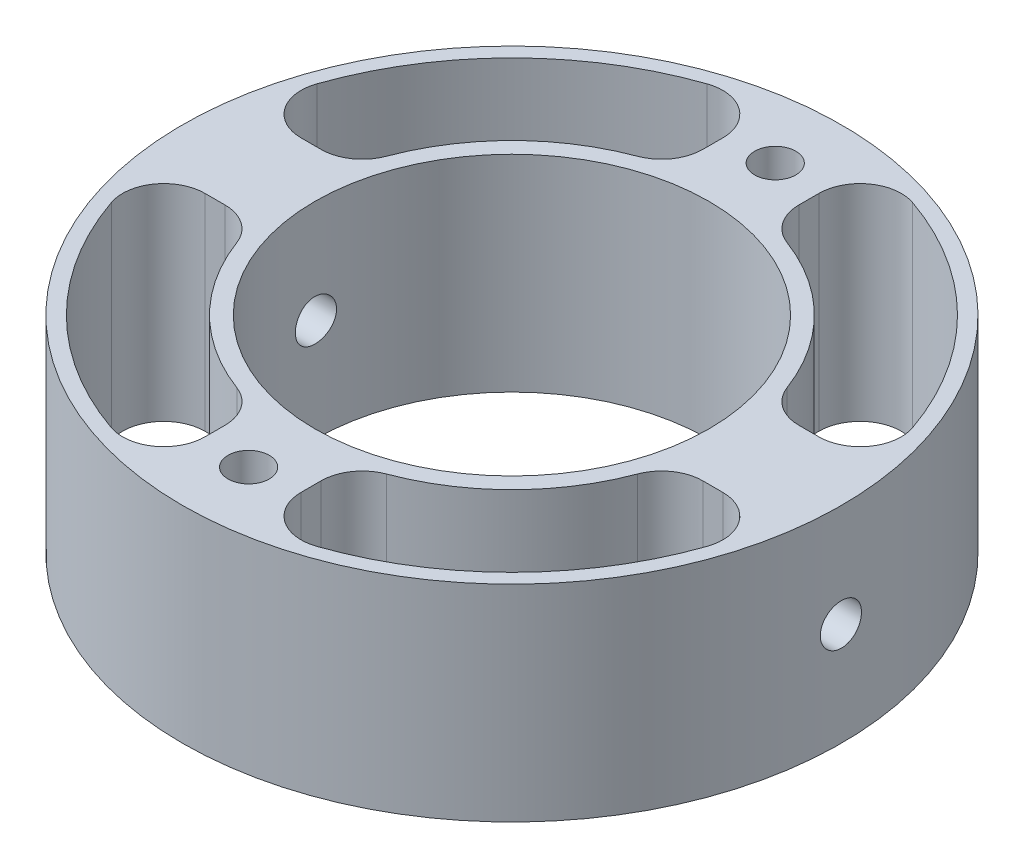
SolidWorks part; units mm, degrees
ref_plane "Front Plane" through (0, 0, 0) normal (0, 0, 1) x (1, 0, 0)
ref_plane "Top Plane" through (0, 0, 0) normal (0, 1, 0) x (1, 0, 0)
ref_plane "Right Plane" through (0, 0, 0) normal (1, 0, 0) x (0, 0, -1)
sketch "Sketch3" plane through (0, 0, 0) normal (0, 1, 0) x (1, 0, 0)
  circle A0 centre (0, 0) radius 24
  circle A1 centre (0, 0) radius 14.35
  dimension "D1" = 48
  dimension "D2" = 28.7
extrude "Boss-Extrude1" add sketch "Sketch3" along normal blind 15
sketch "Sketch4" plane through (0, 0, 0) normal (1, 0, 0) x (0, 0, -1)
  circle A0 centre (0, 7.5) radius 1.5
  dimension "D1" = 3
  dimension "D2" = 7.5
extrude "Cut-Extrude2" cut sketch "Sketch4" against normal blind 100 from offset 50
sketch "Sketch5" plane through (0, 15, 0) normal (0, 1, 0) x (1, 0, 0)
  circle A0 centre (0, 19.175) radius 1.5
  circle A3 centre (0, -19.175) radius 1.5
  dimension "D1" = 3
  dimension "D4" = 3
  dimension "D2" = 19.175
  dimension "D3" = 19.175
extrude "Cut-Extrude3" cut sketch "Sketch5" against normal blind 100
sketch "Sketch7" plane through (0, 15, 0) normal (0, 1, 0) x (1, 0, 0)
  line L0 (3.5, 15.175) -> (3.5, 22.675)
  line L1 (15.175, 3.5) -> (22.675, 3.5)
  arc A0 (3.5, 22.675) -> (22.675, 3.5) centre (0, 0) cw
  arc A1 (3.5, 15.175) -> (15.175, 3.5) centre (0, 0) cw
  dimension "D1" = 3.5
  dimension "D2" = 22.675
  dimension "D4" = 3.5
  dimension "D3" = 3.5
  dimension "D5" = 15.175
  dimension "D6" = 3.5
extrude "Cut-Extrude6" cut sketch "Sketch7" against normal blind 26
sketch "Sketch9" plane through (0, 15, 0) normal (0, 1, 0) x (1, 0, 0)
  line L0 (15.175, -3.5) -> (22.675, -3.5)
  line L1 (3.5, -15.175) -> (3.5, -22.675)
  arc A0 (15.175, -3.5) -> (3.5, -15.175) centre (0, 0) cw
  arc A1 (22.675, -3.5) -> (3.5, -22.675) centre (0, 0) cw
  dimension "D3" = 3.5
  dimension "D6" = 3.5
  dimension "D1" = 15.175
  dimension "D2" = 3.5
  dimension "D4" = 22.675
  dimension "D5" = 3.5
extrude "Cut-Extrude7" cut sketch "Sketch9" against normal blind 26
sketch "Sketch10" plane through (0, 15, 0) normal (0, 1, 0) x (1, 0, 0)
  line L0 (-3.5, 15.175) -> (-3.5, 22.675)
  line L1 (-22.675, 3.5) -> (-15.175, 3.5)
  arc A0 (-3.5, 15.175) -> (-15.175, 3.5) centre (0, 0) ccw
  arc A1 (-3.5, 22.675) -> (-22.675, 3.5) centre (0, 0) ccw
  dimension "D1" = 3.5
  dimension "D4" = 3.5
  dimension "D3" = 3.5
  dimension "D6" = 3.5
  dimension "D2" = 15.175
  dimension "D5" = 22.675
extrude "Cut-Extrude8" cut sketch "Sketch10" against normal blind 26
sketch "Sketch11" plane through (0, 15, 0) normal (0, 1, 0) x (1, 0, 0)
  line L0 (-15.175, -3.5) -> (-22.675, -3.5)
  line L1 (-3.5, -15.175) -> (-3.5, -22.675)
  arc A0 (-22.675, -3.5) -> (-3.5, -22.675) centre (0, 0) ccw
  arc A1 (-3.5, -15.175) -> (-15.175, -3.5) centre (0, 0) cw
  dimension "D4" = 3.5
  dimension "D3" = 3.5
  dimension "D2" = 3.5
  dimension "D5" = 3.5
  dimension "D1" = 22.675
  dimension "D6" = 15.175
extrude "Cut-Extrude9" cut sketch "Sketch11" against normal blind 26
fillet "Fillet5" radius 3 16 edges at (3.5, 7.5, -15.175) (3.5, 7.5, -22.675) (15.175, 7.5, -3.5) (22.675, 7.5, -3.5) (15.175, 7.5, 3.5) (22.675, 7.5, 3.5) (3.5, 7.5, 15.175) (3.5, 7.5, 22.675) (-3.5, 7.5, 22.675) (-3.5, 7.5, 15.175) (-22.675, 7.5, 3.5) (-15.175, 7.5, 3.5) (-15.175, 7.5, -3.5) (-22.675, 7.5, -3.5) (-3.5, 7.5, -15.175) (-3.5, 7.5, -22.675)
equation "\"TubeInnerDiameter\"= 48mm"
equation "\"MotorCasingDiameter\"= 28.7mm"
equation "\"BoltDiameter\"= 3mm"
equation "\"SpacerHeight\"= 15mm"
equation "\"D1@Sketch3\"=\"TubeInnerDiameter\""
equation "\"D1@Boss-Extrude1\"=\"SpacerHeight\""
equation "\"D1@Sketch4\"=\"BoltDiameter\""
equation "\"D2@Sketch4\"=\"SpacerHeight\"/2"
equation "\"TopBoltDiameter\"= 3mm"
equation "\"D1@Sketch5\"=\"TopBoltDiameter\""
equation "\"D2@Sketch5\"=(\"TubeInnerDiameter\"/2-\"MotorCasingDiameter\"/2)/2+\"MotorCasingDiameter\"/2"
equation "\"D4@Sketch5\"=\"TopBoltDiameter\""
equation "\"D3@Sketch5\"=(\"TubeInnerDiameter\"/2-\"MotorCasingDiameter\"/2)/2+\"MotorCasingDiameter\"/2"
equation "\"PressureChannelWidth\"= 8mm"
equation "\"IgniterChannelDiameter\"= 2.8mm"
equation "\"D1@Sketch7\"=\"TopBoltDiameter\"/2+\"BoltChannelSeparation\""
equation "\"D4@Sketch7\"=\"BoltDiameter\"/2+\"BoltChannelSeparation\""
equation "\"BoltChannelSeparation\" = 2mm"
equation "\"D3@Sketch7\"=\"TopBoltDiameter\"/2+\"BoltChannelSeparation\""
equation "\"D5@Sketch7\"=(\"TubeInnerDiameter\"/2+\"MotorCasingDiameter\"/2)/2-\"PressureChannelWidth\"/2"
equation "\"D6@Sketch7\"=\"BoltDiameter\"/2+\"BoltChannelSeparation\""
equation "\"D2@Sketch7\"=(\"TubeInnerDiameter\"/2+\"MotorCasingDiameter\"/2)/2+\"PressureChannelWidth\"/2-0.5"
equation "\"D2@Sketch3\"=\"MotorCasingDiameter\""
equation "\"ChamferRadius\"= 3mm"
equation "\"D1@Sketch9\"=(\"TubeInnerDiameter\"/2+\"MotorCasingDiameter\"/2)/2-\"PressureChannelWidth\"/2"
equation "\"D2@Sketch9\"=\"BoltDiameter\"/2+\"BoltChannelSeparation\""
equation "\"D3@Sketch9\"=\"BoltDiameter\"/2+\"BoltChannelSeparation\""
equation "\"D4@Sketch9\"=(\"TubeInnerDiameter\"/2+\"MotorCasingDiameter\"/2)/2+\"PressureChannelWidth\"/2-0.5mm"
equation "\"D5@Sketch9\"=\"TopBoltDiameter\"/2+\"BoltChannelSeparation\""
equation "\"D6@Sketch9\"=\"TopBoltDiameter\"/2+\"BoltChannelSeparation\""
equation "\"D1@Sketch10\"=\"TopBoltDiameter\"/2+\"BoltChannelSeparation\""
equation "\"D2@Sketch10\"=(\"TubeInnerDiameter\"/2+\"MotorCasingDiameter\"/2)/2-\"PressureChannelWidth\"/2"
equation "\"D3@Sketch10\"=\"BoltDiameter\"/2+\"BoltChannelSeparation\""
equation "\"D4@Sketch10\"=\"TopBoltDiameter\"/2+\"BoltChannelSeparation\""
equation "\"D5@Sketch10\"=(\"TubeInnerDiameter\"/2+\"MotorCasingDiameter\"/2)/2+\"PressureChannelWidth\"/2-0.5mm"
equation "\"D6@Sketch10\"=\"BoltDiameter\"/2+\"BoltChannelSeparation\""
equation "\"D1@Sketch11\"=(\"TubeInnerDiameter\"/2+\"MotorCasingDiameter\"/2)/2+\"PressureChannelWidth\"/2-0.5mm"
equation "\"D2@Sketch11\"=\"BoltDiameter\"/2+\"BoltChannelSeparation\""
equation "\"D3@Sketch11\"=\"TopBoltDiameter\"/2+\"BoltChannelSeparation\""
equation "\"D4@Sketch11\"=\"BoltDiameter\"/2+\"BoltChannelSeparation\""
equation "\"D5@Sketch11\"=\"TopBoltDiameter\"/2+\"BoltChannelSeparation\""
equation "\"D6@Sketch11\"=(\"TubeInnerDiameter\"/2+\"MotorCasingDiameter\"/2)/2-\"PressureChannelWidth\"/2"
equation "\"D1@Fillet5\"=\"ChamferRadius\""
